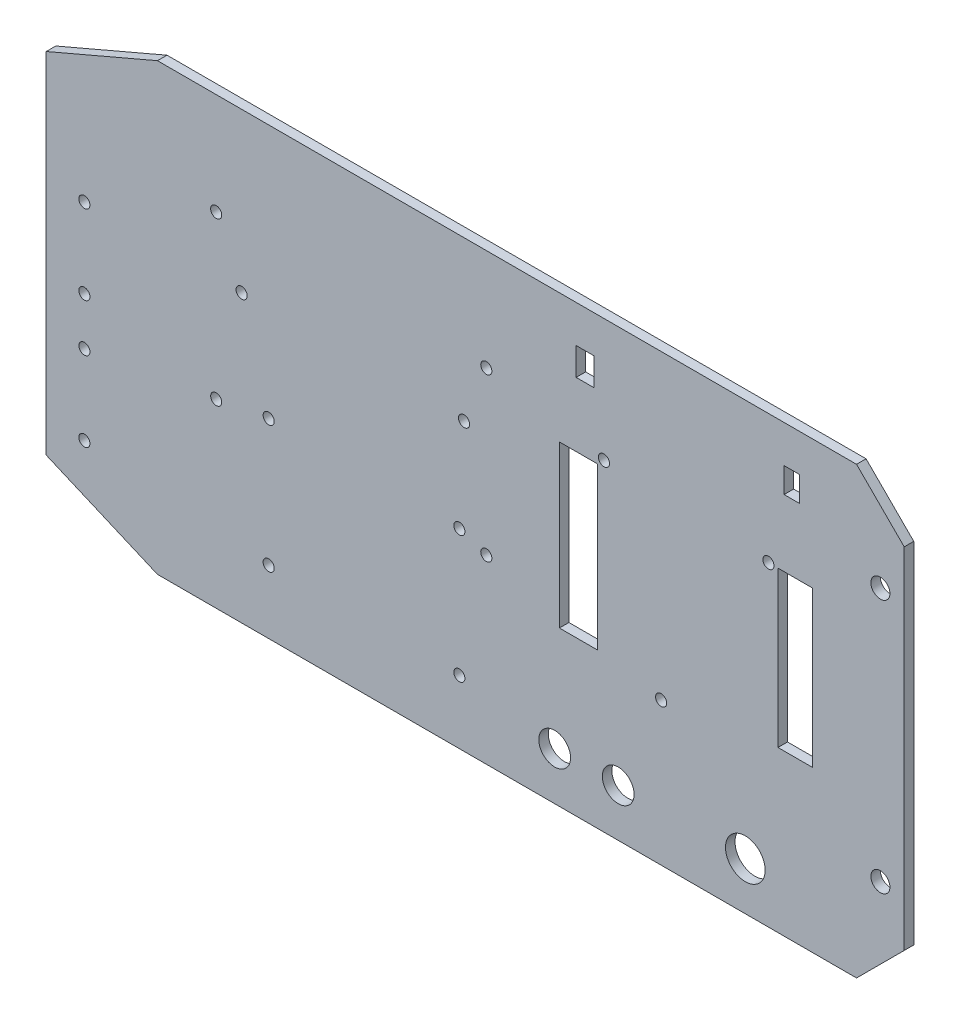
SolidWorks part; units mm, degrees
ref_plane "Front Plane" through (0, 0, 0) normal (0, 0, 1) x (1, 0, 0)
ref_plane "Top Plane" through (0, 0, 0) normal (0, 1, 0) x (1, 0, 0)
ref_plane "Right Plane" through (0, 0, 0) normal (1, 0, 0) x (0, 0, -1)
sketch "Sketch1" plane through (0, 0, 0) normal (0, 0, 1) x (1, 0, 0)
  line L1 (0, 0) -> (270, 0)
  line L2 (0, 0) -> (0, 140)
  line L3 (0, 140) -> (270, 140)
  line L4 (270, 0) -> (270, 140)
  dimension "D1" = 270
  dimension "D2" = 140
extrude "Boss-Extrude1" add sketch "Sketch1" along normal blind 3 contours L3 L4 L1 L2
sketch "Sketch2" plane through (0, 0, 3) normal (0, 0, 1) x (1, 0, 0)
  line L0 (0, 70) -> (270, 70) construction
  line L1 (0, 0) -> (0, 140) construction
  line L2 (270, 0) -> (270, 140) construction
  line L4 (0, 0) -> (270, 0) construction
  line L5 (135, 0) -> (135, 140) construction
  line L6 (0, 140) -> (270, 140) construction
  circle A0 centre (220, 15) radius 6.25
  circle A1 centre (180, 15) radius 5
  circle A2 centre (160, 15) radius 5
  dimension "D1" = 12.5
  dimension "D4" = 10
  dimension "D5" = 10
  dimension "D2" = 50
  dimension "D3" = 15
  dimension "D6" = 15
  dimension "D7" = 15
  dimension "D8" = 20
  dimension "D9" = 40
sketch "Sketch3" plane through (0, 0, 3) normal (0, 0, 1) x (1, 0, 0)
  line L0 (69.999, -65.254) -> (69.999, -51.8181) construction
  line L1 (122.4366, 122.3771) -> (146.1085, 122.3771) construction
extrude "Cut-Extrude1" cut sketch "Sketch2" against normal blind 3
sketch "Sketch5" plane through (0, 0, 3) normal (0, 0, 1) x (1, 0, 0)
  line L0 (255, 140) -> (270, 125)
  line L1 (0, 140) -> (270, 140) construction
  line L2 (270, 0) -> (270, 140) construction
  line L3 (270, 125) -> (270, 140)
  line L4 (270, 140) -> (255, 140)
  line L5 (0, 70) -> (270, 70) construction
  line L6 (0, 0) -> (0, 140) construction
  line L7 (0, 140) -> (0, 125)
  line L8 (0, 125) -> (35, 140)
  line L9 (35, 140) -> (0, 140)
  line L10 (270, 0) -> (255, 0)
  line L11 (270, 15) -> (270, 0)
  line L12 (255, 0) -> (270, 15)
  line L13 (0, 15) -> (35, 0)
  line L14 (0, 0) -> (0, 15)
  line L15 (35, 0) -> (0, 0)
  dimension "D1" = 15
  dimension "D2" = 15
  dimension "D3" = 35
  dimension "D4" = 15
extrude "Cut-Extrude3" cut sketch "Sketch5" against normal blind 3
sketch "Sketch6" plane through (0, 0, 0) normal (0, 0, -1) x (-1, 0, 0)
  line L1 (-161.4837, 48.6264) -> (-173.5028, 48.6264)
  line L2 (-161.4837, 48.6264) -> (-161.4837, 99.3438)
  line L3 (-161.4837, 99.3438) -> (-173.5028, 99.3438)
  line L4 (-173.5028, 48.6264) -> (-173.5028, 99.3438)
  line L5 (-230.2652, 50.4606) -> (-241.1996, 50.4606)
  line L6 (-230.2652, 50.4606) -> (-230.2652, 99.3438)
  line L7 (-230.2652, 99.3438) -> (-241.1996, 99.3438)
  line L8 (-241.1996, 50.4606) -> (-241.1996, 99.3438)
  line L9 (-166.756, 119.5587) -> (-172.4324, 119.5587)
  line L10 (-166.756, 119.5587) -> (-166.756, 128.2481)
  line L11 (-166.756, 128.2481) -> (-172.4324, 128.2481)
  line L12 (-172.4324, 119.5587) -> (-172.4324, 128.2481)
  line L13 (-232.1927, 120.3512) -> (-237.0464, 120.3512)
  line L14 (-232.1927, 120.3512) -> (-232.1927, 128.2481)
  line L15 (-232.1927, 128.2481) -> (-237.0464, 128.2481)
  line L16 (-237.0464, 120.3512) -> (-237.0464, 128.2481)
  point P16 (-166.756, 119.5587)
  point P17 (0, 0)
  point P18 (-237.0464, 120.3512)
extrude "Cut-Extrude5" cut sketch "Sketch6" against normal blind 10
sketch "Sketch7" plane through (0, 0, 0) normal (0, 0, -1) x (-1, 0, 0)
  line L1 (-53.4837, 57) -> (-138.4837, 57) construction
  line L2 (-53.4837, 57) -> (-53.4837, 108) construction
  line L3 (-53.4837, 108) -> (-138.4837, 108) construction
  line L4 (-138.4837, 57) -> (-138.4837, 108) construction
  line L7 (-53.4837, 108) -> (-138.4837, 108) construction
  line L9 (-43.4837, 120) -> (-153.4837, 120) construction
  line L10 (-43.4837, 120) -> (-43.4837, 30) construction
  line L11 (-43.4837, 30) -> (-153.4837, 30) construction
  line L12 (-153.4837, 120) -> (-153.4837, 30) construction
  line L13 (-43.4837, 120) -> (-153.4837, 30) construction
  line L14 (-43.4837, 30) -> (-153.4837, 120) construction
  circle A0 centre (-53.4837, 57) radius 1.75
  circle A1 centre (-138.4837, 57) radius 1.75
  circle A2 centre (-138.4837, 108) radius 1.75
  circle A3 centre (-53.4837, 108) radius 1.75
  point P12 (-98.4837, 75)
  dimension "D1" = 3.5
  dimension "D8" = 3.5
  dimension "D9" = 3.5
  dimension "D10" = 3.5
  dimension "D2" = 90
  dimension "D3" = 110
  dimension "D4" = 10
  dimension "D5" = 27
  dimension "D6" = 12
  dimension "D7" = 15
extrude "Cut-Extrude8" cut sketch "Sketch7" against normal blind 10
sketch "Sketch8" plane through (0, 0, 0) normal (0, 0, -1) x (-1, 0, 0)
  line L0 (-17.5, 7.5) -> (-17.5, 132.5) construction
  line L1 (-35, 0) -> (0, 15) construction
  line L2 (0, 125) -> (-35, 140) construction
  line L3 (-12, 25) -> (-12, 65) construction
  line L4 (-17.5, 70) -> (0, 70) construction
  line L5 (0, 15) -> (0, 125) construction
  line L6 (-12, 50) -> (-12, 70) construction
  circle A0 centre (-12, 25) radius 1.75
  circle A1 centre (-12, 65) radius 1.75
  circle A2 centre (-12, 50) radius 1.75
  circle A3 centre (-12, 90) radius 1.75
  dimension "D1" = 3.5
  dimension "D2" = 3.5
  dimension "D6" = 3.5
  dimension "D3" = 40
  dimension "D4" = 5
  dimension "D5" = 12
  dimension "D7" = 20
extrude "Cut-Extrude9" cut sketch "Sketch8" against normal blind 10
sketch "Sketch9" plane through (0, 0, 0) normal (0, 0, -1) x (-1, 0, 0)
  line L1 (-70, 20) -> (-130, 20) construction
  line L2 (-70, 20) -> (-70, 60) construction
  line L3 (-70, 60) -> (-130, 60) construction
  line L4 (-130, 20) -> (-130, 60) construction
  line L7 (-61.4837, 90) -> (-131.4837, 90) construction
  line L10 (-262.5, 7.5) -> (-262.5, 132.5) construction
  line L11 (-270, 15) -> (-255, 0) construction
  line L12 (-255, 140) -> (-270, 125) construction
  line L13 (-262.5, 70) -> (-270, 70) construction
  line L14 (-270, 15) -> (-270, 125) construction
  circle A0 centre (-70, 20) radius 1.75
  circle A1 centre (-130, 20) radius 1.75
  circle A2 centre (-130, 60) radius 1.75
  circle A3 centre (-70, 60) radius 1.75
  circle A4 centre (-61.4837, 90) radius 1.75
  circle A5 centre (-131.4837, 90) radius 1.75
  circle A6 centre (-262.5, 30) radius 3
  circle A7 centre (-262.5, 110) radius 3
  dimension "D3" = 3.5
  dimension "D4" = 3.5
  dimension "D5" = 3.5
  dimension "D6" = 3.5
  dimension "D7" = 3.5
  dimension "D8" = 3.5
  dimension "D10" = 6
  dimension "D1" = 60
  dimension "D2" = 40
  dimension "D9" = 70
  dimension "D11" = 80
extrude "Cut-Extrude10" cut sketch "Sketch9" against normal blind 10
sketch "Sketch10" plane through (0, 0, 0) normal (0, 0, -1) x (-1, 0, 0)
  circle A1 centre (-193.5028, 45) radius 1.75
  circle A2 centre (-175.5028, 101.3438) radius 1.75
  circle A3 centre (-227.2652, 99.3438) radius 1.75
  point P8 (0, 0)
  dimension "D2" = 3.5
  dimension "D1" = 3.5
  dimension "D3" = 3.5
extrude "Cut-Extrude11" cut sketch "Sketch10" against normal blind 10
